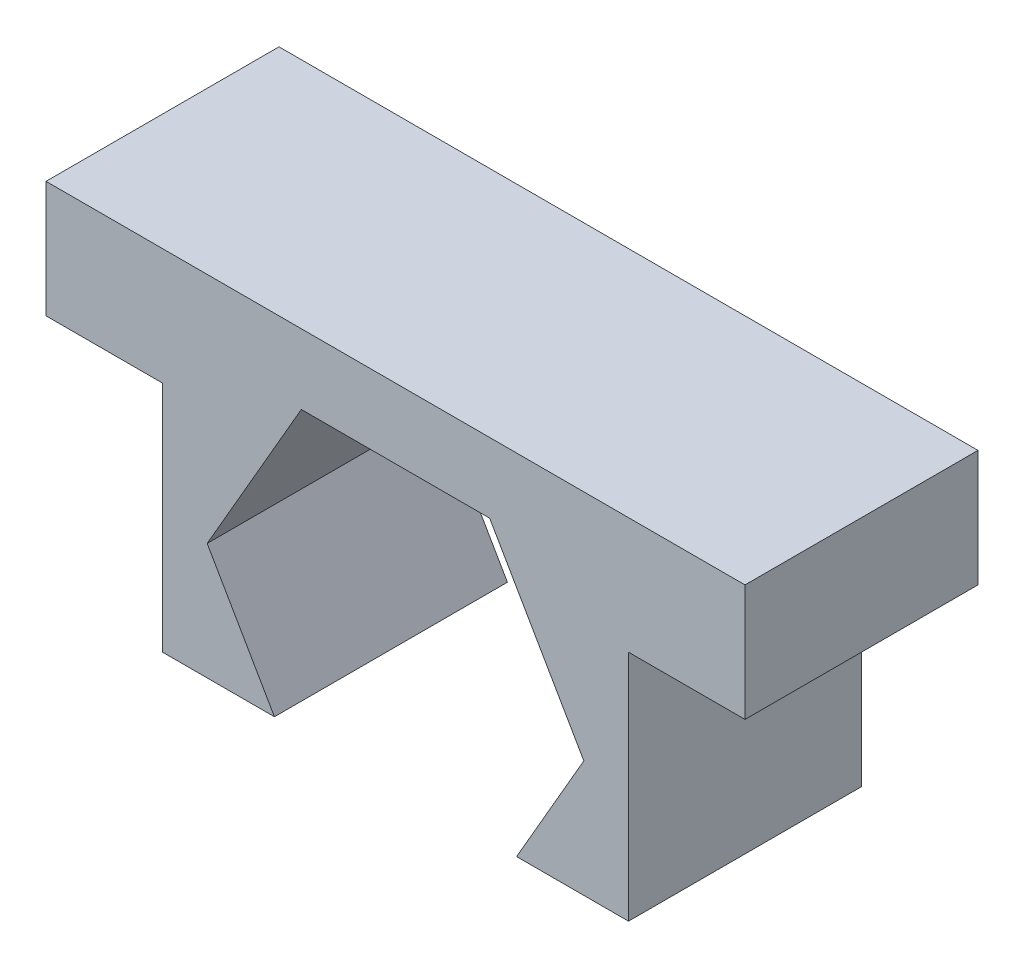
SolidWorks part; units mm, degrees
ref_plane "Front Plane" through (0, 0, 0) normal (0, 0, 1) x (1, 0, 0)
ref_plane "Top Plane" through (0, 0, 0) normal (0, 1, 0) x (1, 0, 0)
ref_plane "Right Plane" through (0, 0, 0) normal (1, 0, 0) x (0, 0, -1)
sketch "Sketch1" plane through (0, 0, 0) normal (0, 0, 1) x (1, 0, 0)
  line L0 (5, 10) -> (5, 12.0192) construction
  line L1 (0, 0) -> (10, 0)
  line L2 (0, 0) -> (0, 10)
  line L3 (0, 10) -> (10, 10)
  line L4 (10, 0) -> (10, 10)
  line L5 (2.9793, 1.5) -> (7.0207, 1.5)
  line L6 (7.0207, 1.5) -> (9.0415, 5)
  line L7 (9.0415, 5) -> (7.0207, 8.5)
  line L8 (7.0207, 8.5) -> (2.9793, 8.5)
  line L9 (2.9793, 8.5) -> (0.9585, 5)
  line L10 (0.9585, 5) -> (2.9793, 1.5)
  line L11 (10, 10) -> (12.5, 10)
  line L12 (10, 10) -> (10, 7.5)
  line L13 (10, 7.5) -> (12.5, 7.5)
  line L14 (12.5, 10) -> (12.5, 7.5)
  line L15 (0, 7.5) -> (-2.5, 7.5)
  line L16 (-2.5, 10) -> (-2.5, 7.5)
  line L17 (0, 10) -> (-2.5, 10)
  line L18 (0, 10) -> (0, 7.5)
  line L19 (0, 2.5) -> (10, 2.5)
  circle A0 centre (5, 5) radius 3.5 construction
  point P14 (0, 5)
  point P16 (5, 0)
  dimension "D1" = 10
  dimension "D2" = 10
  dimension "D3" = 7
  dimension "D4" = 2.5
  dimension "D5" = 2.5
  dimension "D6" = 7.5
extrude "Boss-Extrude1" add sketch "Sketch1" along normal blind 5 contours L1 L4 L3 L2 L10 L9 L8 L7 L6 L5 | L2 L17 L16 L15 | L14 L11 L4 L13
sketch "Sketch2" plane through (0, 0, 5) normal (0, 0, 1) x (1, 0, 0)
  line L0 (16, 7.5) -> (16, 2.5)
  line L1 (16, 2.5) -> (18.4019, 2.5)
  line L2 (18.4019, 2.5) -> (16.9585, 5)
  line L3 (16.9585, 5) -> (18.9793, 8.5)
  line L4 (18.9793, 8.5) -> (23.0207, 8.5)
  line L5 (23.0207, 8.5) -> (25.0415, 5)
  line L6 (25.0415, 5) -> (23.5981, 2.5)
  line L7 (23.5981, 2.5) -> (26, 2.5)
  line L8 (26, 2.5) -> (26, 7.5)
  line L9 (26, 7.5) -> (28.5, 7.5)
  line L10 (28.5, 7.5) -> (28.5, 10)
  line L11 (28.5, 10) -> (13.5, 10)
  line L12 (13.5, 10) -> (13.5, 7.5)
  line L13 (13.5, 7.5) -> (16, 7.5)
  line L14 (0, 7.5) -> (0, 2.5)
  line L15 (0, 2.5) -> (2.4019, 2.5)
  line L16 (2.4019, 2.5) -> (0.9585, 5)
  line L17 (0.9585, 5) -> (2.9793, 8.5)
  line L18 (2.9793, 8.5) -> (7.0207, 8.5)
  line L19 (7.0207, 8.5) -> (9.0415, 5)
  line L20 (9.0415, 5) -> (7.5981, 2.5)
  line L21 (7.5981, 2.5) -> (10, 2.5)
  line L22 (10, 2.5) -> (10, 7.5)
  line L23 (10, 7.5) -> (12.5, 7.5)
  line L24 (12.5, 7.5) -> (12.5, 10)
  line L25 (12.5, 10) -> (-2.5, 10)
  line L26 (-2.5, 10) -> (-2.5, 7.5)
  line L27 (-2.5, 7.5) -> (0, 7.5)
  line L28 (0, 7.5) -> (0, 2.5)
  line L29 (0, 2.5) -> (2.4019, 2.5)
  line L30 (2.4019, 2.5) -> (0.9585, 5)
  line L31 (0.9585, 5) -> (2.9793, 8.5)
  line L32 (2.9793, 8.5) -> (7.0207, 8.5)
  line L33 (7.0207, 8.5) -> (9.0415, 5)
  line L34 (9.0415, 5) -> (7.5981, 2.5)
  line L35 (7.5981, 2.5) -> (10, 2.5)
  line L36 (10, 2.5) -> (10, 7.5)
  line L37 (10, 7.5) -> (12.5, 7.5)
  line L38 (12.5, 7.5) -> (12.5, 10)
  line L39 (12.5, 10) -> (-2.5, 10)
  line L40 (-2.5, 10) -> (-2.5, 7.5)
  line L41 (-2.5, 7.5) -> (0, 7.5)
  line L42 (32, 7.5) -> (32, 2.5)
  line L43 (32, 2.5) -> (34.4019, 2.5)
  line L44 (34.4019, 2.5) -> (32.9585, 5)
  line L45 (32.9585, 5) -> (34.9793, 8.5)
  line L46 (34.9793, 8.5) -> (39.0207, 8.5)
  line L47 (39.0207, 8.5) -> (41.0415, 5)
  line L48 (41.0415, 5) -> (39.5981, 2.5)
  line L49 (39.5981, 2.5) -> (42, 2.5)
  line L50 (42, 2.5) -> (42, 7.5)
  line L51 (42, 7.5) -> (44.5, 7.5)
  line L52 (44.5, 7.5) -> (44.5, 10)
  line L53 (44.5, 10) -> (29.5, 10)
  line L54 (29.5, 10) -> (29.5, 7.5)
  line L55 (29.5, 7.5) -> (32, 7.5)
  line L56 (48, 7.5) -> (48, 2.5)
  line L57 (48, 2.5) -> (50.4019, 2.5)
  line L58 (50.4019, 2.5) -> (48.9585, 5)
  line L59 (48.9585, 5) -> (50.9793, 8.5)
  line L60 (50.9793, 8.5) -> (55.0207, 8.5)
  line L61 (55.0207, 8.5) -> (57.0415, 5)
  line L62 (57.0415, 5) -> (55.5981, 2.5)
  line L63 (55.5981, 2.5) -> (58, 2.5)
  line L64 (58, 2.5) -> (58, 7.5)
  line L65 (58, 7.5) -> (60.5, 7.5)
  line L66 (60.5, 7.5) -> (60.5, 10)
  line L67 (60.5, 10) -> (45.5, 10)
  line L68 (45.5, 10) -> (45.5, 7.5)
  line L69 (45.5, 7.5) -> (48, 7.5)
  line L70 (64, 7.5) -> (64, 2.5)
  line L71 (64, 2.5) -> (66.4019, 2.5)
  line L72 (66.4019, 2.5) -> (64.9585, 5)
  line L73 (64.9585, 5) -> (66.9793, 8.5)
  line L74 (66.9793, 8.5) -> (71.0207, 8.5)
  line L75 (71.0207, 8.5) -> (73.0415, 5)
  line L76 (73.0415, 5) -> (71.5981, 2.5)
  line L77 (71.5981, 2.5) -> (74, 2.5)
  line L78 (74, 2.5) -> (74, 7.5)
  line L79 (74, 7.5) -> (76.5, 7.5)
  line L80 (76.5, 7.5) -> (76.5, 10)
  line L81 (76.5, 10) -> (61.5, 10)
  line L82 (61.5, 10) -> (61.5, 7.5)
  line L83 (61.5, 7.5) -> (64, 7.5)
  line L84 (80, 7.5) -> (80, 2.5)
  line L85 (80, 2.5) -> (82.4019, 2.5)
  line L86 (82.4019, 2.5) -> (80.9585, 5)
  line L87 (80.9585, 5) -> (82.9793, 8.5)
  line L88 (82.9793, 8.5) -> (87.0207, 8.5)
  line L89 (87.0207, 8.5) -> (89.0415, 5)
  line L90 (89.0415, 5) -> (87.5981, 2.5)
  line L91 (87.5981, 2.5) -> (90, 2.5)
  line L92 (90, 2.5) -> (90, 7.5)
  line L93 (90, 7.5) -> (92.5, 7.5)
  line L94 (92.5, 7.5) -> (92.5, 10)
  line L95 (92.5, 10) -> (77.5, 10)
  line L96 (77.5, 10) -> (77.5, 7.5)
  line L97 (77.5, 7.5) -> (80, 7.5)
  line L98 (96, 7.5) -> (96, 2.5)
  line L99 (96, 2.5) -> (98.4019, 2.5)
  line L100 (98.4019, 2.5) -> (96.9585, 5)
  line L101 (96.9585, 5) -> (98.9793, 8.5)
  line L102 (98.9793, 8.5) -> (103.0207, 8.5)
  line L103 (103.0207, 8.5) -> (105.0415, 5)
  line L104 (105.0415, 5) -> (103.5981, 2.5)
  line L105 (103.5981, 2.5) -> (106, 2.5)
  line L106 (106, 2.5) -> (106, 7.5)
  line L107 (106, 7.5) -> (108.5, 7.5)
  line L108 (108.5, 7.5) -> (108.5, 10)
  line L109 (108.5, 10) -> (93.5, 10)
  line L110 (93.5, 10) -> (93.5, 7.5)
  line L111 (93.5, 7.5) -> (96, 7.5)
  line L112 (16, 16.5) -> (16, 11.5)
  line L113 (16, 11.5) -> (18.4019, 11.5)
  line L114 (18.4019, 11.5) -> (16.9585, 14)
  line L115 (16.9585, 14) -> (18.9793, 17.5)
  line L116 (18.9793, 17.5) -> (23.0207, 17.5)
  line L117 (23.0207, 17.5) -> (25.0415, 14)
  line L118 (25.0415, 14) -> (23.5981, 11.5)
  line L119 (23.5981, 11.5) -> (26, 11.5)
  line L120 (26, 11.5) -> (26, 16.5)
  line L121 (26, 16.5) -> (28.5, 16.5)
  line L122 (28.5, 16.5) -> (28.5, 19)
  line L123 (28.5, 19) -> (13.5, 19)
  line L124 (13.5, 19) -> (13.5, 16.5)
  line L125 (13.5, 16.5) -> (16, 16.5)
  line L126 (32, 16.5) -> (32, 11.5)
  line L127 (32, 11.5) -> (34.4019, 11.5)
  line L128 (34.4019, 11.5) -> (32.9585, 14)
  line L129 (32.9585, 14) -> (34.9793, 17.5)
  line L130 (34.9793, 17.5) -> (39.0207, 17.5)
  line L131 (39.0207, 17.5) -> (41.0415, 14)
  line L132 (41.0415, 14) -> (39.5981, 11.5)
  line L133 (39.5981, 11.5) -> (42, 11.5)
  line L134 (42, 11.5) -> (42, 16.5)
  line L135 (42, 16.5) -> (44.5, 16.5)
  line L136 (44.5, 16.5) -> (44.5, 19)
  line L137 (44.5, 19) -> (29.5, 19)
  line L138 (29.5, 19) -> (29.5, 16.5)
  line L139 (29.5, 16.5) -> (32, 16.5)
  line L140 (48, 16.5) -> (48, 11.5)
  line L141 (48, 11.5) -> (50.4019, 11.5)
  line L142 (50.4019, 11.5) -> (48.9585, 14)
  line L143 (48.9585, 14) -> (50.9793, 17.5)
  line L144 (50.9793, 17.5) -> (55.0207, 17.5)
  line L145 (55.0207, 17.5) -> (57.0415, 14)
  line L146 (57.0415, 14) -> (55.5981, 11.5)
  line L147 (55.5981, 11.5) -> (58, 11.5)
  line L148 (58, 11.5) -> (58, 16.5)
  line L149 (58, 16.5) -> (60.5, 16.5)
  line L150 (60.5, 16.5) -> (60.5, 19)
  line L151 (60.5, 19) -> (45.5, 19)
  line L152 (45.5, 19) -> (45.5, 16.5)
  line L153 (45.5, 16.5) -> (48, 16.5)
  line L154 (64, 16.5) -> (64, 11.5)
  line L155 (64, 11.5) -> (66.4019, 11.5)
  line L156 (66.4019, 11.5) -> (64.9585, 14)
  line L157 (64.9585, 14) -> (66.9793, 17.5)
  line L158 (66.9793, 17.5) -> (71.0207, 17.5)
  line L159 (71.0207, 17.5) -> (73.0415, 14)
  line L160 (73.0415, 14) -> (71.5981, 11.5)
  line L161 (71.5981, 11.5) -> (74, 11.5)
  line L162 (74, 11.5) -> (74, 16.5)
  line L163 (74, 16.5) -> (76.5, 16.5)
  line L164 (76.5, 16.5) -> (76.5, 19)
  line L165 (76.5, 19) -> (61.5, 19)
  line L166 (61.5, 19) -> (61.5, 16.5)
  line L167 (61.5, 16.5) -> (64, 16.5)
  line L168 (80, 16.5) -> (80, 11.5)
  line L169 (80, 11.5) -> (82.4019, 11.5)
  line L170 (82.4019, 11.5) -> (80.9585, 14)
  line L171 (80.9585, 14) -> (82.9793, 17.5)
  line L172 (82.9793, 17.5) -> (87.0207, 17.5)
  line L173 (87.0207, 17.5) -> (89.0415, 14)
  line L174 (89.0415, 14) -> (87.5981, 11.5)
  line L175 (87.5981, 11.5) -> (90, 11.5)
  line L176 (90, 11.5) -> (90, 16.5)
  line L177 (90, 16.5) -> (92.5, 16.5)
  line L178 (92.5, 16.5) -> (92.5, 19)
  line L179 (92.5, 19) -> (77.5, 19)
  line L180 (77.5, 19) -> (77.5, 16.5)
  line L181 (77.5, 16.5) -> (80, 16.5)
  line L182 (96, 16.5) -> (96, 11.5)
  line L183 (96, 11.5) -> (98.4019, 11.5)
  line L184 (98.4019, 11.5) -> (96.9585, 14)
  line L185 (96.9585, 14) -> (98.9793, 17.5)
  line L186 (98.9793, 17.5) -> (103.0207, 17.5)
  line L187 (103.0207, 17.5) -> (105.0415, 14)
  line L188 (105.0415, 14) -> (103.5981, 11.5)
  line L189 (103.5981, 11.5) -> (106, 11.5)
  line L190 (106, 11.5) -> (106, 16.5)
  line L191 (106, 16.5) -> (108.5, 16.5)
  line L192 (108.5, 16.5) -> (108.5, 19)
  line L193 (108.5, 19) -> (93.5, 19)
  line L194 (93.5, 19) -> (93.5, 16.5)
  line L195 (93.5, 16.5) -> (96, 16.5)
  line L196 (16, 25.5) -> (16, 20.5)
  line L197 (16, 20.5) -> (18.4019, 20.5)
  line L198 (18.4019, 20.5) -> (16.9585, 23)
  line L199 (16.9585, 23) -> (18.9793, 26.5)
  line L200 (18.9793, 26.5) -> (23.0207, 26.5)
  line L201 (23.0207, 26.5) -> (25.0415, 23)
  line L202 (25.0415, 23) -> (23.5981, 20.5)
  line L203 (23.5981, 20.5) -> (26, 20.5)
  line L204 (26, 20.5) -> (26, 25.5)
  line L205 (26, 25.5) -> (28.5, 25.5)
  line L206 (28.5, 25.5) -> (28.5, 28)
  line L207 (28.5, 28) -> (13.5, 28)
  line L208 (13.5, 28) -> (13.5, 25.5)
  line L209 (13.5, 25.5) -> (16, 25.5)
  line L210 (32, 25.5) -> (32, 20.5)
  line L211 (32, 20.5) -> (34.4019, 20.5)
  line L212 (34.4019, 20.5) -> (32.9585, 23)
  line L213 (32.9585, 23) -> (34.9793, 26.5)
  line L214 (34.9793, 26.5) -> (39.0207, 26.5)
  line L215 (39.0207, 26.5) -> (41.0415, 23)
  line L216 (41.0415, 23) -> (39.5981, 20.5)
  line L217 (39.5981, 20.5) -> (42, 20.5)
  line L218 (42, 20.5) -> (42, 25.5)
  line L219 (42, 25.5) -> (44.5, 25.5)
  line L220 (44.5, 25.5) -> (44.5, 28)
  line L221 (44.5, 28) -> (29.5, 28)
  line L222 (29.5, 28) -> (29.5, 25.5)
  line L223 (29.5, 25.5) -> (32, 25.5)
  line L224 (48, 25.5) -> (48, 20.5)
  line L225 (48, 20.5) -> (50.4019, 20.5)
  line L226 (50.4019, 20.5) -> (48.9585, 23)
  line L227 (48.9585, 23) -> (50.9793, 26.5)
  line L228 (50.9793, 26.5) -> (55.0207, 26.5)
  line L229 (55.0207, 26.5) -> (57.0415, 23)
  line L230 (57.0415, 23) -> (55.5981, 20.5)
  line L231 (55.5981, 20.5) -> (58, 20.5)
  line L232 (58, 20.5) -> (58, 25.5)
  line L233 (58, 25.5) -> (60.5, 25.5)
  line L234 (60.5, 25.5) -> (60.5, 28)
  line L235 (60.5, 28) -> (45.5, 28)
  line L236 (45.5, 28) -> (45.5, 25.5)
  line L237 (45.5, 25.5) -> (48, 25.5)
  line L238 (64, 25.5) -> (64, 20.5)
  line L239 (64, 20.5) -> (66.4019, 20.5)
  line L240 (66.4019, 20.5) -> (64.9585, 23)
  line L241 (64.9585, 23) -> (66.9793, 26.5)
  line L242 (66.9793, 26.5) -> (71.0207, 26.5)
  line L243 (71.0207, 26.5) -> (73.0415, 23)
  line L244 (73.0415, 23) -> (71.5981, 20.5)
  line L245 (71.5981, 20.5) -> (74, 20.5)
  line L246 (74, 20.5) -> (74, 25.5)
  line L247 (74, 25.5) -> (76.5, 25.5)
  line L248 (76.5, 25.5) -> (76.5, 28)
  line L249 (76.5, 28) -> (61.5, 28)
  line L250 (61.5, 28) -> (61.5, 25.5)
  line L251 (61.5, 25.5) -> (64, 25.5)
  line L252 (80, 25.5) -> (80, 20.5)
  line L253 (80, 20.5) -> (82.4019, 20.5)
  line L254 (82.4019, 20.5) -> (80.9585, 23)
  line L255 (80.9585, 23) -> (82.9793, 26.5)
  line L256 (82.9793, 26.5) -> (87.0207, 26.5)
  line L257 (87.0207, 26.5) -> (89.0415, 23)
  line L258 (89.0415, 23) -> (87.5981, 20.5)
  line L259 (87.5981, 20.5) -> (90, 20.5)
  line L260 (90, 20.5) -> (90, 25.5)
  line L261 (90, 25.5) -> (92.5, 25.5)
  line L262 (92.5, 25.5) -> (92.5, 28)
  line L263 (92.5, 28) -> (77.5, 28)
  line L264 (77.5, 28) -> (77.5, 25.5)
  line L265 (77.5, 25.5) -> (80, 25.5)
  line L266 (96, 25.5) -> (96, 20.5)
  line L267 (96, 20.5) -> (98.4019, 20.5)
  line L268 (98.4019, 20.5) -> (96.9585, 23)
  line L269 (96.9585, 23) -> (98.9793, 26.5)
  line L270 (98.9793, 26.5) -> (103.0207, 26.5)
  line L271 (103.0207, 26.5) -> (105.0415, 23)
  line L272 (105.0415, 23) -> (103.5981, 20.5)
  line L273 (103.5981, 20.5) -> (106, 20.5)
  line L274 (106, 20.5) -> (106, 25.5)
  line L275 (106, 25.5) -> (108.5, 25.5)
  line L276 (108.5, 25.5) -> (108.5, 28)
  line L277 (108.5, 28) -> (93.5, 28)
  line L278 (93.5, 28) -> (93.5, 25.5)
  line L279 (93.5, 25.5) -> (96, 25.5)
  line L280 (16, 34.5) -> (16, 29.5)
  line L281 (16, 29.5) -> (18.4019, 29.5)
  line L282 (18.4019, 29.5) -> (16.9585, 32)
  line L283 (16.9585, 32) -> (18.9793, 35.5)
  line L284 (18.9793, 35.5) -> (23.0207, 35.5)
  line L285 (23.0207, 35.5) -> (25.0415, 32)
  line L286 (25.0415, 32) -> (23.5981, 29.5)
  line L287 (23.5981, 29.5) -> (26, 29.5)
  line L288 (26, 29.5) -> (26, 34.5)
  line L289 (26, 34.5) -> (28.5, 34.5)
  line L290 (28.5, 34.5) -> (28.5, 37)
  line L291 (28.5, 37) -> (13.5, 37)
  line L292 (13.5, 37) -> (13.5, 34.5)
  line L293 (13.5, 34.5) -> (16, 34.5)
  line L294 (32, 34.5) -> (32, 29.5)
  line L295 (32, 29.5) -> (34.4019, 29.5)
  line L296 (34.4019, 29.5) -> (32.9585, 32)
  line L297 (32.9585, 32) -> (34.9793, 35.5)
  line L298 (34.9793, 35.5) -> (39.0207, 35.5)
  line L299 (39.0207, 35.5) -> (41.0415, 32)
  line L300 (41.0415, 32) -> (39.5981, 29.5)
  line L301 (39.5981, 29.5) -> (42, 29.5)
  line L302 (42, 29.5) -> (42, 34.5)
  line L303 (42, 34.5) -> (44.5, 34.5)
  line L304 (44.5, 34.5) -> (44.5, 37)
  line L305 (44.5, 37) -> (29.5, 37)
  line L306 (29.5, 37) -> (29.5, 34.5)
  line L307 (29.5, 34.5) -> (32, 34.5)
  line L308 (48, 34.5) -> (48, 29.5)
  line L309 (48, 29.5) -> (50.4019, 29.5)
  line L310 (50.4019, 29.5) -> (48.9585, 32)
  line L311 (48.9585, 32) -> (50.9793, 35.5)
  line L312 (50.9793, 35.5) -> (55.0207, 35.5)
  line L313 (55.0207, 35.5) -> (57.0415, 32)
  line L314 (57.0415, 32) -> (55.5981, 29.5)
  line L315 (55.5981, 29.5) -> (58, 29.5)
  line L316 (58, 29.5) -> (58, 34.5)
  line L317 (58, 34.5) -> (60.5, 34.5)
  line L318 (60.5, 34.5) -> (60.5, 37)
  line L319 (60.5, 37) -> (45.5, 37)
  line L320 (45.5, 37) -> (45.5, 34.5)
  line L321 (45.5, 34.5) -> (48, 34.5)
  line L322 (64, 34.5) -> (64, 29.5)
  line L323 (64, 29.5) -> (66.4019, 29.5)
  line L324 (66.4019, 29.5) -> (64.9585, 32)
  line L325 (64.9585, 32) -> (66.9793, 35.5)
  line L326 (66.9793, 35.5) -> (71.0207, 35.5)
  line L327 (71.0207, 35.5) -> (73.0415, 32)
  line L328 (73.0415, 32) -> (71.5981, 29.5)
  line L329 (71.5981, 29.5) -> (74, 29.5)
  line L330 (74, 29.5) -> (74, 34.5)
  line L331 (74, 34.5) -> (76.5, 34.5)
  line L332 (76.5, 34.5) -> (76.5, 37)
  line L333 (76.5, 37) -> (61.5, 37)
  line L334 (61.5, 37) -> (61.5, 34.5)
  line L335 (61.5, 34.5) -> (64, 34.5)
  line L336 (80, 34.5) -> (80, 29.5)
  line L337 (80, 29.5) -> (82.4019, 29.5)
  line L338 (82.4019, 29.5) -> (80.9585, 32)
  line L339 (80.9585, 32) -> (82.9793, 35.5)
  line L340 (82.9793, 35.5) -> (87.0207, 35.5)
  line L341 (87.0207, 35.5) -> (89.0415, 32)
  line L342 (89.0415, 32) -> (87.5981, 29.5)
  line L343 (87.5981, 29.5) -> (90, 29.5)
  line L344 (90, 29.5) -> (90, 34.5)
  line L345 (90, 34.5) -> (92.5, 34.5)
  line L346 (92.5, 34.5) -> (92.5, 37)
  line L347 (92.5, 37) -> (77.5, 37)
  line L348 (77.5, 37) -> (77.5, 34.5)
  line L349 (77.5, 34.5) -> (80, 34.5)
  line L350 (96, 34.5) -> (96, 29.5)
  line L351 (96, 29.5) -> (98.4019, 29.5)
  line L352 (98.4019, 29.5) -> (96.9585, 32)
  line L353 (96.9585, 32) -> (98.9793, 35.5)
  line L354 (98.9793, 35.5) -> (103.0207, 35.5)
  line L355 (103.0207, 35.5) -> (105.0415, 32)
  line L356 (105.0415, 32) -> (103.5981, 29.5)
  line L357 (103.5981, 29.5) -> (106, 29.5)
  line L358 (106, 29.5) -> (106, 34.5)
  line L359 (106, 34.5) -> (108.5, 34.5)
  line L360 (108.5, 34.5) -> (108.5, 37)
  line L361 (108.5, 37) -> (93.5, 37)
  line L362 (93.5, 37) -> (93.5, 34.5)
  line L363 (93.5, 34.5) -> (96, 34.5)
  line L364 (16, 43.5) -> (16, 38.5)
  line L365 (16, 38.5) -> (18.4019, 38.5)
  line L366 (18.4019, 38.5) -> (16.9585, 41)
  line L367 (16.9585, 41) -> (18.9793, 44.5)
  line L368 (18.9793, 44.5) -> (23.0207, 44.5)
  line L369 (23.0207, 44.5) -> (25.0415, 41)
  line L370 (25.0415, 41) -> (23.5981, 38.5)
  line L371 (23.5981, 38.5) -> (26, 38.5)
  line L372 (26, 38.5) -> (26, 43.5)
  line L373 (26, 43.5) -> (28.5, 43.5)
  line L374 (28.5, 43.5) -> (28.5, 46)
  line L375 (28.5, 46) -> (13.5, 46)
  line L376 (13.5, 46) -> (13.5, 43.5)
  line L377 (13.5, 43.5) -> (16, 43.5)
  line L378 (32, 43.5) -> (32, 38.5)
  line L379 (32, 38.5) -> (34.4019, 38.5)
  line L380 (34.4019, 38.5) -> (32.9585, 41)
  line L381 (32.9585, 41) -> (34.9793, 44.5)
  line L382 (34.9793, 44.5) -> (39.0207, 44.5)
  line L383 (39.0207, 44.5) -> (41.0415, 41)
  line L384 (41.0415, 41) -> (39.5981, 38.5)
  line L385 (39.5981, 38.5) -> (42, 38.5)
  line L386 (42, 38.5) -> (42, 43.5)
  line L387 (42, 43.5) -> (44.5, 43.5)
  line L388 (44.5, 43.5) -> (44.5, 46)
  line L389 (44.5, 46) -> (29.5, 46)
  line L390 (29.5, 46) -> (29.5, 43.5)
  line L391 (29.5, 43.5) -> (32, 43.5)
  line L392 (48, 43.5) -> (48, 38.5)
  line L393 (48, 38.5) -> (50.4019, 38.5)
  line L394 (50.4019, 38.5) -> (48.9585, 41)
  line L395 (48.9585, 41) -> (50.9793, 44.5)
  line L396 (50.9793, 44.5) -> (55.0207, 44.5)
  line L397 (55.0207, 44.5) -> (57.0415, 41)
  line L398 (57.0415, 41) -> (55.5981, 38.5)
  line L399 (55.5981, 38.5) -> (58, 38.5)
  line L400 (58, 38.5) -> (58, 43.5)
  line L401 (58, 43.5) -> (60.5, 43.5)
  line L402 (60.5, 43.5) -> (60.5, 46)
  line L403 (60.5, 46) -> (45.5, 46)
  line L404 (45.5, 46) -> (45.5, 43.5)
  line L405 (45.5, 43.5) -> (48, 43.5)
  line L406 (64, 43.5) -> (64, 38.5)
  line L407 (64, 38.5) -> (66.4019, 38.5)
  line L408 (66.4019, 38.5) -> (64.9585, 41)
  line L409 (64.9585, 41) -> (66.9793, 44.5)
  line L410 (66.9793, 44.5) -> (71.0207, 44.5)
  line L411 (71.0207, 44.5) -> (73.0415, 41)
  line L412 (73.0415, 41) -> (71.5981, 38.5)
  line L413 (71.5981, 38.5) -> (74, 38.5)
  line L414 (74, 38.5) -> (74, 43.5)
  line L415 (74, 43.5) -> (76.5, 43.5)
  line L416 (76.5, 43.5) -> (76.5, 46)
  line L417 (76.5, 46) -> (61.5, 46)
  line L418 (61.5, 46) -> (61.5, 43.5)
  line L419 (61.5, 43.5) -> (64, 43.5)
  line L420 (80, 43.5) -> (80, 38.5)
  line L421 (80, 38.5) -> (82.4019, 38.5)
  line L422 (82.4019, 38.5) -> (80.9585, 41)
  line L423 (80.9585, 41) -> (82.9793, 44.5)
  line L424 (82.9793, 44.5) -> (87.0207, 44.5)
  line L425 (87.0207, 44.5) -> (89.0415, 41)
  line L426 (89.0415, 41) -> (87.5981, 38.5)
  line L427 (87.5981, 38.5) -> (90, 38.5)
  line L428 (90, 38.5) -> (90, 43.5)
  line L429 (90, 43.5) -> (92.5, 43.5)
  line L430 (92.5, 43.5) -> (92.5, 46)
  line L431 (92.5, 46) -> (77.5, 46)
  line L432 (77.5, 46) -> (77.5, 43.5)
  line L433 (77.5, 43.5) -> (80, 43.5)
  line L434 (96, 43.5) -> (96, 38.5)
  line L435 (96, 38.5) -> (98.4019, 38.5)
  line L436 (98.4019, 38.5) -> (96.9585, 41)
  line L437 (96.9585, 41) -> (98.9793, 44.5)
  line L438 (98.9793, 44.5) -> (103.0207, 44.5)
  line L439 (103.0207, 44.5) -> (105.0415, 41)
  line L440 (105.0415, 41) -> (103.5981, 38.5)
  line L441 (103.5981, 38.5) -> (106, 38.5)
  line L442 (106, 38.5) -> (106, 43.5)
  line L443 (106, 43.5) -> (108.5, 43.5)
  line L444 (108.5, 43.5) -> (108.5, 46)
  line L445 (108.5, 46) -> (93.5, 46)
  line L446 (93.5, 46) -> (93.5, 43.5)
  line L447 (93.5, 43.5) -> (96, 43.5)
  line L448 (16, 52.5) -> (16, 47.5)
  line L449 (16, 47.5) -> (18.4019, 47.5)
  line L450 (18.4019, 47.5) -> (16.9585, 50)
  line L451 (16.9585, 50) -> (18.9793, 53.5)
  line L452 (18.9793, 53.5) -> (23.0207, 53.5)
  line L453 (23.0207, 53.5) -> (25.0415, 50)
  line L454 (25.0415, 50) -> (23.5981, 47.5)
  line L455 (23.5981, 47.5) -> (26, 47.5)
  line L456 (26, 47.5) -> (26, 52.5)
  line L457 (26, 52.5) -> (28.5, 52.5)
  line L458 (28.5, 52.5) -> (28.5, 55)
  line L459 (28.5, 55) -> (13.5, 55)
  line L460 (13.5, 55) -> (13.5, 52.5)
  line L461 (13.5, 52.5) -> (16, 52.5)
  line L462 (32, 52.5) -> (32, 47.5)
  line L463 (32, 47.5) -> (34.4019, 47.5)
  line L464 (34.4019, 47.5) -> (32.9585, 50)
  line L465 (32.9585, 50) -> (34.9793, 53.5)
  line L466 (34.9793, 53.5) -> (39.0207, 53.5)
  line L467 (39.0207, 53.5) -> (41.0415, 50)
  line L468 (41.0415, 50) -> (39.5981, 47.5)
  line L469 (39.5981, 47.5) -> (42, 47.5)
  line L470 (42, 47.5) -> (42, 52.5)
  line L471 (42, 52.5) -> (44.5, 52.5)
  line L472 (44.5, 52.5) -> (44.5, 55)
  line L473 (44.5, 55) -> (29.5, 55)
  line L474 (29.5, 55) -> (29.5, 52.5)
  line L475 (29.5, 52.5) -> (32, 52.5)
  line L476 (48, 52.5) -> (48, 47.5)
  line L477 (48, 47.5) -> (50.4019, 47.5)
  line L478 (50.4019, 47.5) -> (48.9585, 50)
  line L479 (48.9585, 50) -> (50.9793, 53.5)
  line L480 (50.9793, 53.5) -> (55.0207, 53.5)
  line L481 (55.0207, 53.5) -> (57.0415, 50)
  line L482 (57.0415, 50) -> (55.5981, 47.5)
  line L483 (55.5981, 47.5) -> (58, 47.5)
  line L484 (58, 47.5) -> (58, 52.5)
  line L485 (58, 52.5) -> (60.5, 52.5)
  line L486 (60.5, 52.5) -> (60.5, 55)
  line L487 (60.5, 55) -> (45.5, 55)
  line L488 (45.5, 55) -> (45.5, 52.5)
  line L489 (45.5, 52.5) -> (48, 52.5)
  line L490 (64, 52.5) -> (64, 47.5)
  line L491 (64, 47.5) -> (66.4019, 47.5)
  line L492 (66.4019, 47.5) -> (64.9585, 50)
  line L493 (64.9585, 50) -> (66.9793, 53.5)
  line L494 (66.9793, 53.5) -> (71.0207, 53.5)
  line L495 (71.0207, 53.5) -> (73.0415, 50)
  line L496 (73.0415, 50) -> (71.5981, 47.5)
  line L497 (71.5981, 47.5) -> (74, 47.5)
  line L498 (74, 47.5) -> (74, 52.5)
  line L499 (74, 52.5) -> (76.5, 52.5)
  line L500 (76.5, 52.5) -> (76.5, 55)
  line L501 (76.5, 55) -> (61.5, 55)
  line L502 (61.5, 55) -> (61.5, 52.5)
  line L503 (61.5, 52.5) -> (64, 52.5)
  line L504 (80, 52.5) -> (80, 47.5)
  line L505 (80, 47.5) -> (82.4019, 47.5)
  line L506 (82.4019, 47.5) -> (80.9585, 50)
  line L507 (80.9585, 50) -> (82.9793, 53.5)
  line L508 (82.9793, 53.5) -> (87.0207, 53.5)
  line L509 (87.0207, 53.5) -> (89.0415, 50)
  line L510 (89.0415, 50) -> (87.5981, 47.5)
  line L511 (87.5981, 47.5) -> (90, 47.5)
  line L512 (90, 47.5) -> (90, 52.5)
  line L513 (90, 52.5) -> (92.5, 52.5)
  line L514 (92.5, 52.5) -> (92.5, 55)
  line L515 (92.5, 55) -> (77.5, 55)
  line L516 (77.5, 55) -> (77.5, 52.5)
  line L517 (77.5, 52.5) -> (80, 52.5)
  line L518 (96, 52.5) -> (96, 47.5)
  line L519 (96, 47.5) -> (98.4019, 47.5)
  line L520 (98.4019, 47.5) -> (96.9585, 50)
  line L521 (96.9585, 50) -> (98.9793, 53.5)
  line L522 (98.9793, 53.5) -> (103.0207, 53.5)
  line L523 (103.0207, 53.5) -> (105.0415, 50)
  line L524 (105.0415, 50) -> (103.5981, 47.5)
  line L525 (103.5981, 47.5) -> (106, 47.5)
  line L526 (106, 47.5) -> (106, 52.5)
  line L527 (106, 52.5) -> (108.5, 52.5)
  line L528 (108.5, 52.5) -> (108.5, 55)
  line L529 (108.5, 55) -> (93.5, 55)
  line L530 (93.5, 55) -> (93.5, 52.5)
  line L531 (93.5, 52.5) -> (96, 52.5)
  line L532 (16, 61.5) -> (16, 56.5)
  line L533 (16, 56.5) -> (18.4019, 56.5)
  line L534 (18.4019, 56.5) -> (16.9585, 59)
  line L535 (16.9585, 59) -> (18.9793, 62.5)
  line L536 (18.9793, 62.5) -> (23.0207, 62.5)
  line L537 (23.0207, 62.5) -> (25.0415, 59)
  line L538 (25.0415, 59) -> (23.5981, 56.5)
  line L539 (23.5981, 56.5) -> (26, 56.5)
  line L540 (26, 56.5) -> (26, 61.5)
  line L541 (26, 61.5) -> (28.5, 61.5)
  line L542 (28.5, 61.5) -> (28.5, 64)
  line L543 (28.5, 64) -> (13.5, 64)
  line L544 (13.5, 64) -> (13.5, 61.5)
  line L545 (13.5, 61.5) -> (16, 61.5)
  line L546 (32, 61.5) -> (32, 56.5)
  line L547 (32, 56.5) -> (34.4019, 56.5)
  line L548 (34.4019, 56.5) -> (32.9585, 59)
  line L549 (32.9585, 59) -> (34.9793, 62.5)
  line L550 (34.9793, 62.5) -> (39.0207, 62.5)
  line L551 (39.0207, 62.5) -> (41.0415, 59)
  line L552 (41.0415, 59) -> (39.5981, 56.5)
  line L553 (39.5981, 56.5) -> (42, 56.5)
  line L554 (42, 56.5) -> (42, 61.5)
  line L555 (42, 61.5) -> (44.5, 61.5)
  line L556 (44.5, 61.5) -> (44.5, 64)
  line L557 (44.5, 64) -> (29.5, 64)
  line L558 (29.5, 64) -> (29.5, 61.5)
  line L559 (29.5, 61.5) -> (32, 61.5)
  line L560 (48, 61.5) -> (48, 56.5)
  line L561 (48, 56.5) -> (50.4019, 56.5)
  line L562 (50.4019, 56.5) -> (48.9585, 59)
  line L563 (48.9585, 59) -> (50.9793, 62.5)
  line L564 (50.9793, 62.5) -> (55.0207, 62.5)
  line L565 (55.0207, 62.5) -> (57.0415, 59)
  line L566 (57.0415, 59) -> (55.5981, 56.5)
  line L567 (55.5981, 56.5) -> (58, 56.5)
  line L568 (58, 56.5) -> (58, 61.5)
  line L569 (58, 61.5) -> (60.5, 61.5)
  line L570 (60.5, 61.5) -> (60.5, 64)
  line L571 (60.5, 64) -> (45.5, 64)
  line L572 (45.5, 64) -> (45.5, 61.5)
  line L573 (45.5, 61.5) -> (48, 61.5)
  line L574 (64, 61.5) -> (64, 56.5)
  line L575 (64, 56.5) -> (66.4019, 56.5)
  line L576 (66.4019, 56.5) -> (64.9585, 59)
  line L577 (64.9585, 59) -> (66.9793, 62.5)
  line L578 (66.9793, 62.5) -> (71.0207, 62.5)
  line L579 (71.0207, 62.5) -> (73.0415, 59)
  line L580 (73.0415, 59) -> (71.5981, 56.5)
  line L581 (71.5981, 56.5) -> (74, 56.5)
  line L582 (74, 56.5) -> (74, 61.5)
  line L583 (74, 61.5) -> (76.5, 61.5)
  line L584 (76.5, 61.5) -> (76.5, 64)
  line L585 (76.5, 64) -> (61.5, 64)
  line L586 (61.5, 64) -> (61.5, 61.5)
  line L587 (61.5, 61.5) -> (64, 61.5)
  line L588 (80, 61.5) -> (80, 56.5)
  line L589 (80, 56.5) -> (82.4019, 56.5)
  line L590 (82.4019, 56.5) -> (80.9585, 59)
  line L591 (80.9585, 59) -> (82.9793, 62.5)
  line L592 (82.9793, 62.5) -> (87.0207, 62.5)
  line L593 (87.0207, 62.5) -> (89.0415, 59)
  line L594 (89.0415, 59) -> (87.5981, 56.5)
  line L595 (87.5981, 56.5) -> (90, 56.5)
  line L596 (90, 56.5) -> (90, 61.5)
  line L597 (90, 61.5) -> (92.5, 61.5)
  line L598 (92.5, 61.5) -> (92.5, 64)
  line L599 (92.5, 64) -> (77.5, 64)
  line L600 (77.5, 64) -> (77.5, 61.5)
  line L601 (77.5, 61.5) -> (80, 61.5)
  line L602 (96, 61.5) -> (96, 56.5)
  line L603 (96, 56.5) -> (98.4019, 56.5)
  line L604 (98.4019, 56.5) -> (96.9585, 59)
  line L605 (96.9585, 59) -> (98.9793, 62.5)
  line L606 (98.9793, 62.5) -> (103.0207, 62.5)
  line L607 (103.0207, 62.5) -> (105.0415, 59)
  line L608 (105.0415, 59) -> (103.5981, 56.5)
  line L609 (103.5981, 56.5) -> (106, 56.5)
  line L610 (106, 56.5) -> (106, 61.5)
  line L611 (106, 61.5) -> (108.5, 61.5)
  line L612 (108.5, 61.5) -> (108.5, 64)
  line L613 (108.5, 64) -> (93.5, 64)
  line L614 (93.5, 64) -> (93.5, 61.5)
  line L615 (93.5, 61.5) -> (96, 61.5)
  line L616 (0, 16.5) -> (0, 11.5)
  line L617 (0, 11.5) -> (2.4019, 11.5)
  line L618 (2.4019, 11.5) -> (0.9585, 14)
  line L619 (0.9585, 14) -> (2.9793, 17.5)
  line L620 (2.9793, 17.5) -> (7.0207, 17.5)
  line L621 (7.0207, 17.5) -> (9.0415, 14)
  line L622 (9.0415, 14) -> (7.5981, 11.5)
  line L623 (7.5981, 11.5) -> (10, 11.5)
  line L624 (10, 11.5) -> (10, 16.5)
  line L625 (10, 16.5) -> (12.5, 16.5)
  line L626 (12.5, 16.5) -> (12.5, 19)
  line L627 (12.5, 19) -> (-2.5, 19)
  line L628 (-2.5, 19) -> (-2.5, 16.5)
  line L629 (-2.5, 16.5) -> (0, 16.5)
  line L630 (0, 25.5) -> (0, 20.5)
  line L631 (0, 20.5) -> (2.4019, 20.5)
  line L632 (2.4019, 20.5) -> (0.9585, 23)
  line L633 (0.9585, 23) -> (2.9793, 26.5)
  line L634 (2.9793, 26.5) -> (7.0207, 26.5)
  line L635 (7.0207, 26.5) -> (9.0415, 23)
  line L636 (9.0415, 23) -> (7.5981, 20.5)
  line L637 (7.5981, 20.5) -> (10, 20.5)
  line L638 (10, 20.5) -> (10, 25.5)
  line L639 (10, 25.5) -> (12.5, 25.5)
  line L640 (12.5, 25.5) -> (12.5, 28)
  line L641 (12.5, 28) -> (-2.5, 28)
  line L642 (-2.5, 28) -> (-2.5, 25.5)
  line L643 (-2.5, 25.5) -> (0, 25.5)
  line L644 (0, 34.5) -> (0, 29.5)
  line L645 (0, 29.5) -> (2.4019, 29.5)
  line L646 (2.4019, 29.5) -> (0.9585, 32)
  line L647 (0.9585, 32) -> (2.9793, 35.5)
  line L648 (2.9793, 35.5) -> (7.0207, 35.5)
  line L649 (7.0207, 35.5) -> (9.0415, 32)
  line L650 (9.0415, 32) -> (7.5981, 29.5)
  line L651 (7.5981, 29.5) -> (10, 29.5)
  line L652 (10, 29.5) -> (10, 34.5)
  line L653 (10, 34.5) -> (12.5, 34.5)
  line L654 (12.5, 34.5) -> (12.5, 37)
  line L655 (12.5, 37) -> (-2.5, 37)
  line L656 (-2.5, 37) -> (-2.5, 34.5)
  line L657 (-2.5, 34.5) -> (0, 34.5)
  line L658 (0, 43.5) -> (0, 38.5)
  line L659 (0, 38.5) -> (2.4019, 38.5)
  line L660 (2.4019, 38.5) -> (0.9585, 41)
  line L661 (0.9585, 41) -> (2.9793, 44.5)
  line L662 (2.9793, 44.5) -> (7.0207, 44.5)
  line L663 (7.0207, 44.5) -> (9.0415, 41)
  line L664 (9.0415, 41) -> (7.5981, 38.5)
  line L665 (7.5981, 38.5) -> (10, 38.5)
  line L666 (10, 38.5) -> (10, 43.5)
  line L667 (10, 43.5) -> (12.5, 43.5)
  line L668 (12.5, 43.5) -> (12.5, 46)
  line L669 (12.5, 46) -> (-2.5, 46)
  line L670 (-2.5, 46) -> (-2.5, 43.5)
  line L671 (-2.5, 43.5) -> (0, 43.5)
  line L672 (0, 52.5) -> (0, 47.5)
  line L673 (0, 47.5) -> (2.4019, 47.5)
  line L674 (2.4019, 47.5) -> (0.9585, 50)
  line L675 (0.9585, 50) -> (2.9793, 53.5)
  line L676 (2.9793, 53.5) -> (7.0207, 53.5)
  line L677 (7.0207, 53.5) -> (9.0415, 50)
  line L678 (9.0415, 50) -> (7.5981, 47.5)
  line L679 (7.5981, 47.5) -> (10, 47.5)
  line L680 (10, 47.5) -> (10, 52.5)
  line L681 (10, 52.5) -> (12.5, 52.5)
  line L682 (12.5, 52.5) -> (12.5, 55)
  line L683 (12.5, 55) -> (-2.5, 55)
  line L684 (-2.5, 55) -> (-2.5, 52.5)
  line L685 (-2.5, 52.5) -> (0, 52.5)
  line L686 (0, 61.5) -> (0, 56.5)
  line L687 (0, 56.5) -> (2.4019, 56.5)
  line L688 (2.4019, 56.5) -> (0.9585, 59)
  line L689 (0.9585, 59) -> (2.9793, 62.5)
  line L690 (2.9793, 62.5) -> (7.0207, 62.5)
  line L691 (7.0207, 62.5) -> (9.0415, 59)
  line L692 (9.0415, 59) -> (7.5981, 56.5)
  line L693 (7.5981, 56.5) -> (10, 56.5)
  line L694 (10, 56.5) -> (10, 61.5)
  line L695 (10, 61.5) -> (12.5, 61.5)
  line L696 (12.5, 61.5) -> (12.5, 64)
  line L697 (12.5, 64) -> (-2.5, 64)
  line L698 (-2.5, 64) -> (-2.5, 61.5)
  line L699 (-2.5, 61.5) -> (0, 61.5)
  dimension "D1" = 0
  dimension "D2" = 7
  dimension "D3" = 7
extrude "Boss-Extrude2" [suppressed] add sketch "Sketch2" against normal blind 5
